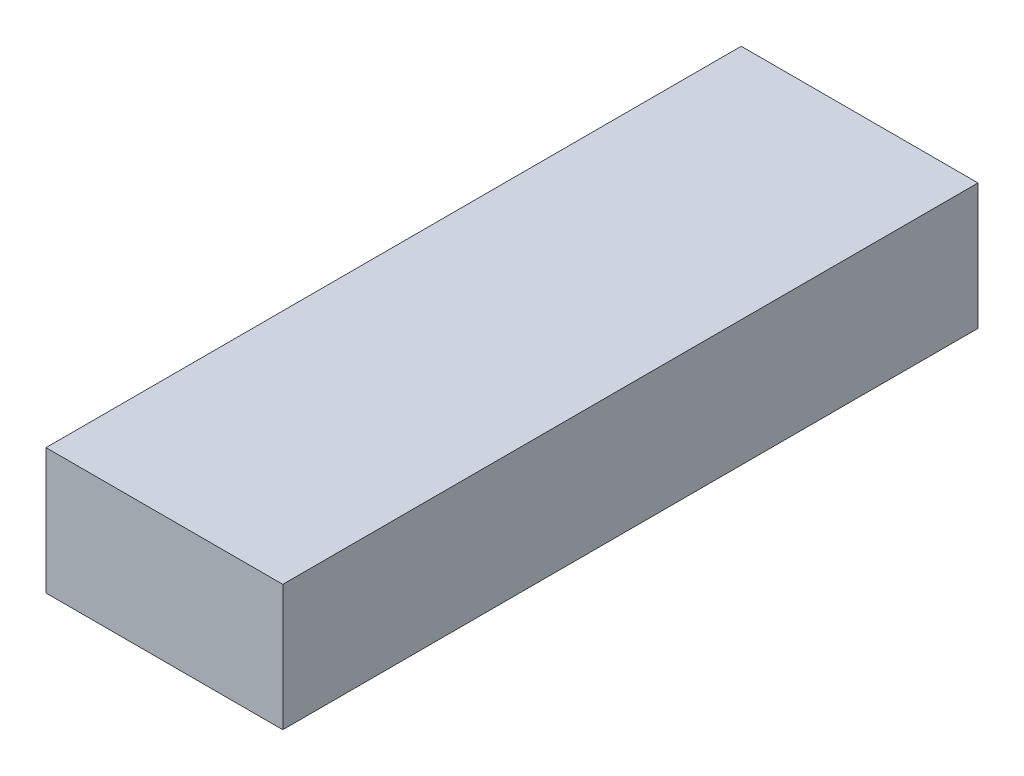
SolidWorks part; units mm, degrees
material "Custom Plastic"
ref_plane "Front Plane" through (0, 0, 0) normal (0, 0, 1) x (1, 0, 0)
ref_plane "Top Plane" through (0, 0, 0) normal (0, 1, 0) x (1, 0, 0)
ref_plane "Right Plane" through (0, 0, 0) normal (1, 0, 0) x (0, 0, -1)
sketch "Sketch1" plane through (0, 0, 0) normal (0, 1, 0) x (1, 0, 0)
  line L1 (-23.5, -69) -> (23.5, -69)
  line L2 (-23.5, -69) -> (-23.5, 69)
  line L3 (-23.5, 69) -> (23.5, 69)
  line L4 (23.5, -69) -> (23.5, 69)
  line L5 (-23.5, -69) -> (23.5, 69) construction
  line L6 (-23.5, 69) -> (23.5, -69) construction
  point P0 (0, 0)
  dimension "D1" = 138
  dimension "D2" = 47
extrude "Boss-Extrude1" add sketch "Sketch1" along normal blind 25
